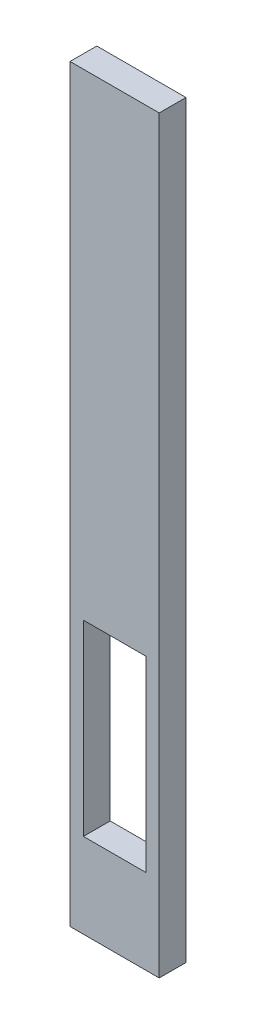
SolidWorks part; units mm, degrees
ref_plane "Plano frontal" through (0, 0, 0) normal (0, 0, 1) x (1, 0, 0)
ref_plane "Plano superior" through (0, 0, 0) normal (0, 1, 0) x (1, 0, 0)
ref_plane "Plano direito" through (0, 0, 0) normal (1, 0, 0) x (0, 0, -1)
sketch "Esboço1" plane through (0, 0, 0) normal (0, 0, 1) x (1, 0, 0)
  line L0 (-9.7071, 51.5723) -> (-9.7071, -32.4277)
  line L1 (-9.7071, 51.5723) -> (0.2929, 51.5723)
  line L2 (-9.7071, -32.4277) -> (0.2929, -32.4277)
  line L3 (0.2929, 51.5723) -> (0.2929, -32.4277)
  line L4 (-9.7071, 42.5723) -> (0.2929, 42.5723)
  line L5 (-9.7071, -23.4277) -> (0.2929, -23.4277)
  line L7 (-8.2071, -1.9277) -> (-1.2071, -1.9277)
  line L8 (-8.2071, -1.9277) -> (-8.2071, -22.9277)
  line L9 (-8.2071, -22.9277) -> (-1.2071, -22.9277)
  line L10 (-1.2071, -1.9277) -> (-1.2071, -22.9277)
  point P8 (-2.7144, 34.6819)
  point P10 (-4.7071, -23.4277)
  point P14 (-1.2071, -12.4277)
  dimension "D1" = 84
  dimension "D2" = 9
  dimension "D3" = 9
  dimension "D4" = 10
  dimension "D5" = 11
  dimension "D6" = 21
  dimension "D7" = 7
extrude "Ressalto-extrusão1" add sketch "Esboço1" along normal blind 3 contours L0 L4 L3 L1 | L0 L5 L3 L4 L7 L10 L9 L8 | L5 L0 L2 L3
